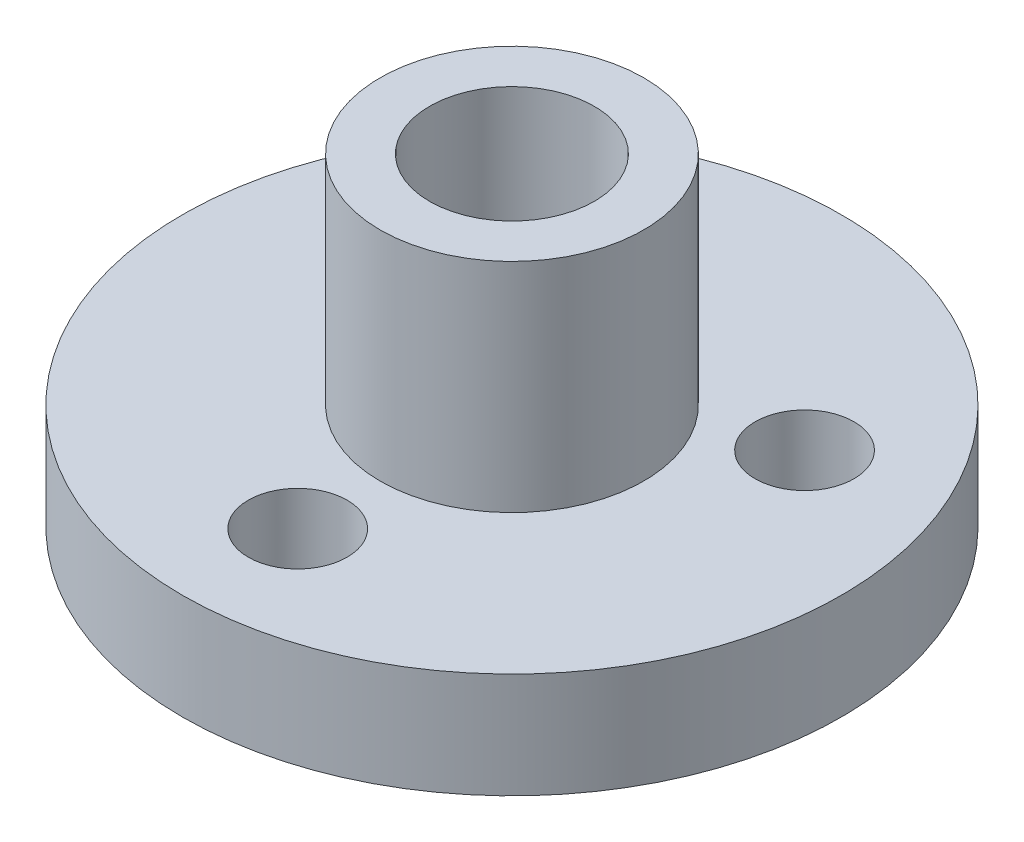
SolidWorks part; units mm, degrees
ref_plane "Plano frontal" through (0, 0, 0) normal (0, 0, 1) x (1, 0, 0)
ref_plane "Plano superior" through (0, 0, 0) normal (0, 1, 0) x (1, 0, 0)
ref_plane "Plano direito" through (0, 0, 0) normal (1, 0, 0) x (0, 0, -1)
sketch "Esboço1" plane through (0, 0, 0) normal (0, 1, 0) x (1, 0, 0)
  line L0 (0, 18.0869) -> (0, -15.8951) construction
  line L1 (-19.095, 0) -> (17.0916, 0) construction
  circle A0 centre (0, 0) radius 10
  circle A1 centre (0, 0) radius 2.5
  dimension "D1" = 20
  dimension "D2" = 5
extrude "Ressalto-extrusão1" add sketch "Esboço1" along normal blind 3.2
sketch "Esboço2" plane through (0, 0, 0) normal (0, -1, 0) x (1, 0, 0)
  line L0 (-12.7617, 0) -> (14.526, 0) construction
  line L1 (0, 13.8791) -> (0, -13.0557) construction
  circle A0 centre (0, 0) radius 6.5 construction
  circle A1 centre (0, 6.5) radius 1.5
  dimension "D1" = 13
  dimension "D2" = 3
extrude "Corte-extrusão1" cut sketch "Esboço2" against normal up to next (3.2 mm away)
pattern_circular "PadrãoCircular1" count 3 over 360 about axis through (0, 0, 0) along (0, 1, 0) of "Corte-extrusão1"
sketch "Esboço3" plane through (0, 3.2, 0) normal (0, 1, 0) x (1, 0, 0)
  circle A0 centre (0, 0) radius 4
  circle A1 centre (0, 0) radius 2.5 construction
  circle A2 centre (0, 0) radius 2.5
  dimension "D1" = 8
extrude "Ressalto-extrusão2" add sketch "Esboço3" along normal blind 6.6
